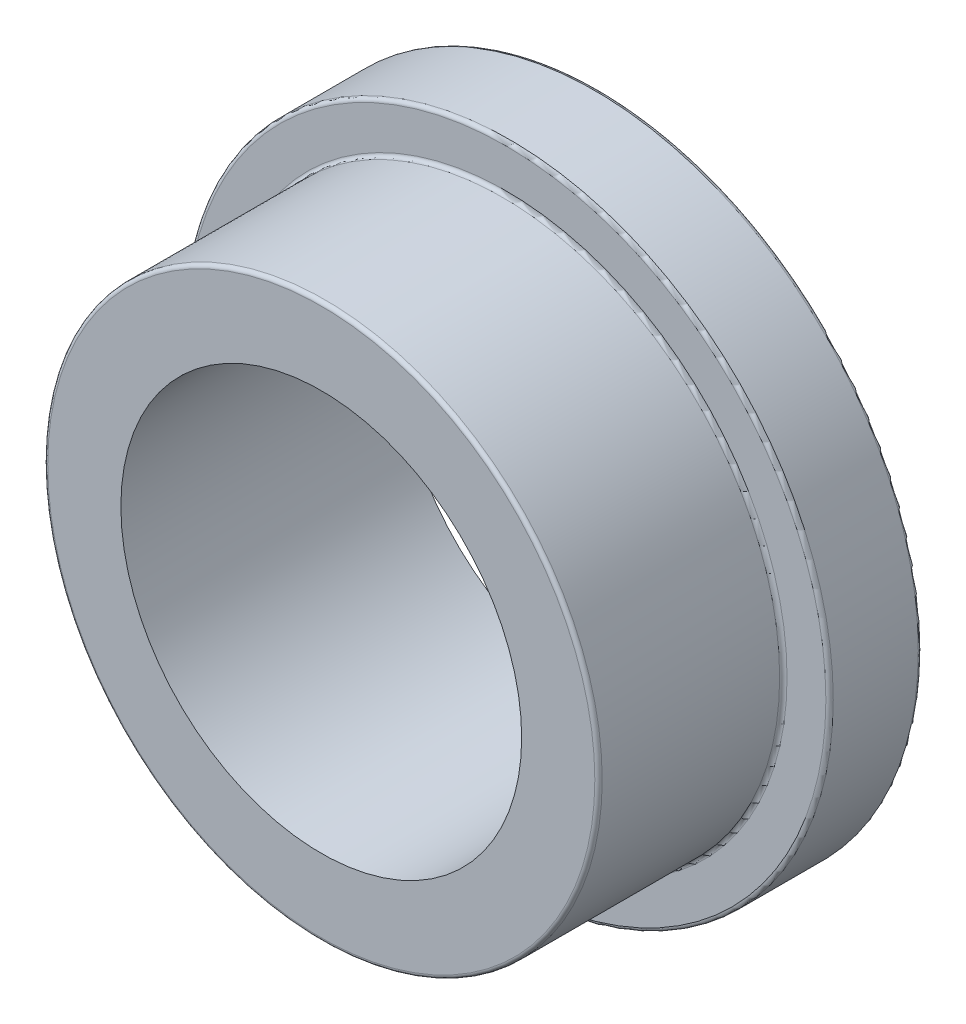
SolidWorks part; units mm, degrees
material "Nylon 101"
ref_plane "Front Plane" through (0, 0, 0) normal (0, 0, 1) x (1, 0, 0)
ref_plane "Top Plane" through (0, 0, 0) normal (0, 1, 0) x (1, 0, 0)
ref_plane "Right Plane" through (0, 0, 0) normal (1, 0, 0) x (0, 0, -1)
sketch "Sketch1" plane through (0, 0, 0) normal (0, 1, 0) x (1, 0, 0)
  line L0 (6.885, -6.35) -> (9.525, -6.35)
  line L1 (9.525, -6.35) -> (9.525, 0)
  line L2 (9.525, 0) -> (11.1125, 0)
  line L3 (11.1125, 0) -> (11.1125, 3.175)
  line L4 (11.1125, 3.175) -> (6.885, 3.175)
  line L5 (6.885, 3.175) -> (6.885, -6.35)
  line L6 (0, 3.175) -> (0, -6.35) construction
  dimension "D1" = 6.885
  dimension "D2" = 9.525
  dimension "D3" = 11.1125
  dimension "D4" = 6.35
  dimension "D5" = 9.525
revolve "Revolve1" add sketch "Sketch1" angle 360 about L6
fillet "Minor Fillet Smoothing" radius 0.127 4 edges at (9.525, 0, 0) (9.525, 0, 6.35) (11.1125, 0, 0) (11.1125, 0, -3.175)
